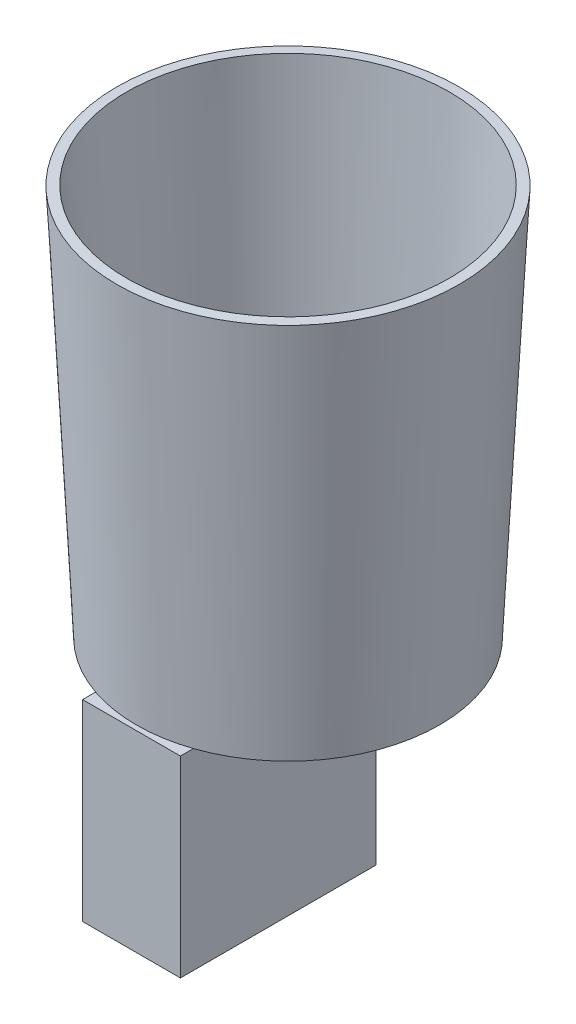
SolidWorks part; units mm, degrees
ref_plane "Front Plane" through (0, 0, 0) normal (0, 0, 1) x (1, 0, 0)
ref_plane "Top Plane" through (0, 0, 0) normal (0, 1, 0) x (1, 0, 0)
ref_plane "Right Plane" through (0, 0, 0) normal (1, 0, 0) x (0, 0, -1)
sketch "Sketch1" plane through (0, 0, 0) normal (0, 0, 1) x (1, 0, 0)
  line L0 (0, 0) -> (-31, 0)
  line L1 (-31, 0) -> (-35, 80)
  line L2 (0, 0) -> (0, 57.9426) construction
  line L3 (0, 2) -> (-29.0975, 2)
  line L4 (-29.0975, 2) -> (-33.0025, 80.0999)
  line L5 (-33.0025, 80.0999) -> (-35, 80)
  line L6 (0, 0) -> (0, 2)
  dimension "D1" = 31
  dimension "D2" = 80
  dimension "D3" = 4
  dimension "D4" = 2
revolve "Revolve1" add sketch "Sketch1" angle 360 about L2
sketch "Sketch2" plane through (0, 0, 0) normal (0, -1, 0) x (1, 0, 0)
  circle A0 centre (-17.55, 0) radius 12.5
  dimension "D1" = 25
extrude "Cut-Extrude1" cut sketch "Sketch2" against normal blind 10
sketch "Sketch3" plane through (0, 0, 0) normal (0, -1, 0) x (1, 0, 0)
  line L1 (10, 32) -> (-10, 32)
  line L2 (10, 32) -> (10, -8)
  line L3 (10, -8) -> (-10, -8)
  line L4 (-10, 32) -> (-10, -8)
  line L5 (10, -8) -> (0, -8) construction
  line L6 (10, -8) -> (10, 0) construction
  line L7 (10, 0) -> (0, 0) construction
  line L8 (0, -8) -> (0, 0) construction
  circle A0 centre (0, 0) radius 3.5375
  point P9 (0, -8)
  dimension "D1" = 40
  dimension "D2" = 20
  dimension "D3" = 8
extrude "Boss-Extrude1" add sketch "Sketch3" along normal blind 39.3
